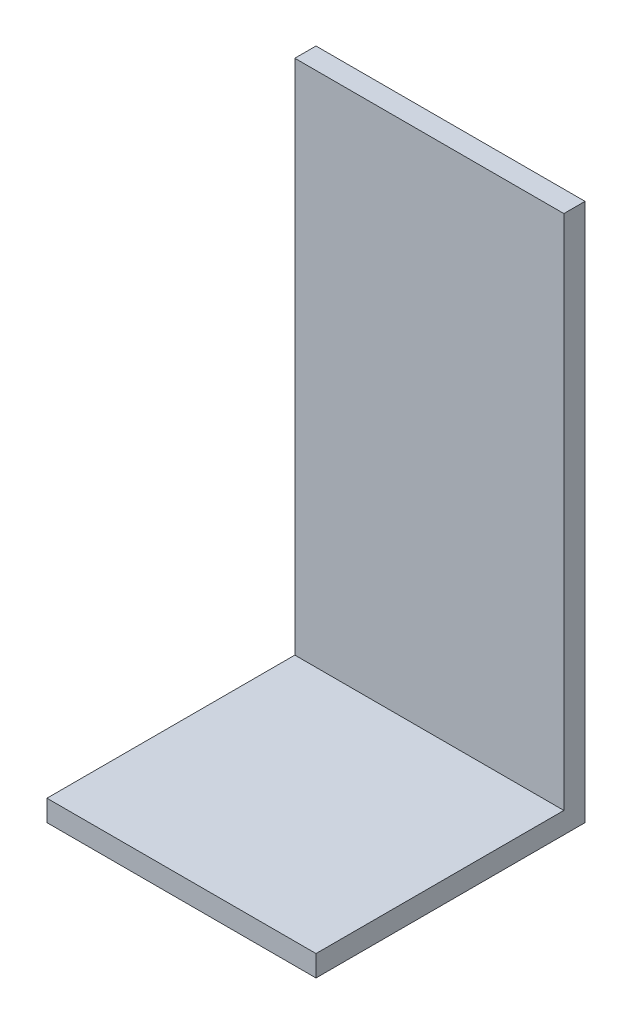
SolidWorks part; units mm, degrees
ref_plane "Front Plane" through (0, 0, 0) normal (0, 0, 1) x (1, 0, 0)
ref_plane "Top Plane" through (0, 0, 0) normal (0, 1, 0) x (1, 0, 0)
ref_plane "Right Plane" through (0, 0, 0) normal (1, 0, 0) x (0, 0, -1)
sketch "Sketch1" plane through (0, 0, 0) normal (0, 1, 0) x (1, 0, 0)
  line L1 (-13.1204, 11.1245) -> (12.2796, 11.1245)
  line L2 (-13.1204, 11.1245) -> (-13.1204, -14.2755)
  line L3 (-13.1204, -14.2755) -> (12.2796, -14.2755)
  line L4 (12.2796, 11.1245) -> (12.2796, -14.2755)
  dimension "D1" = 25.4
extrude "Boss-Extrude1" add sketch "Sketch1" along normal blind 2
sketch "Sketch2" plane through (0, 2, 0) normal (0, 1, 0) x (1, 0, 0)
  line L0 (12.2796, -14.2755) -> (12.2796, 11.1245) construction
  line L1 (-13.1204, 11.1245) -> (12.2796, 11.1245)
  line L2 (-13.1204, 11.1245) -> (-13.1204, 9.1245)
  line L3 (-13.1204, 9.1245) -> (12.2796, 9.1245)
  line L4 (12.2796, 11.1245) -> (12.2796, 9.1245)
  dimension "D1" = 2
extrude "Boss-Extrude2" add sketch "Sketch2" along normal blind 48.8
